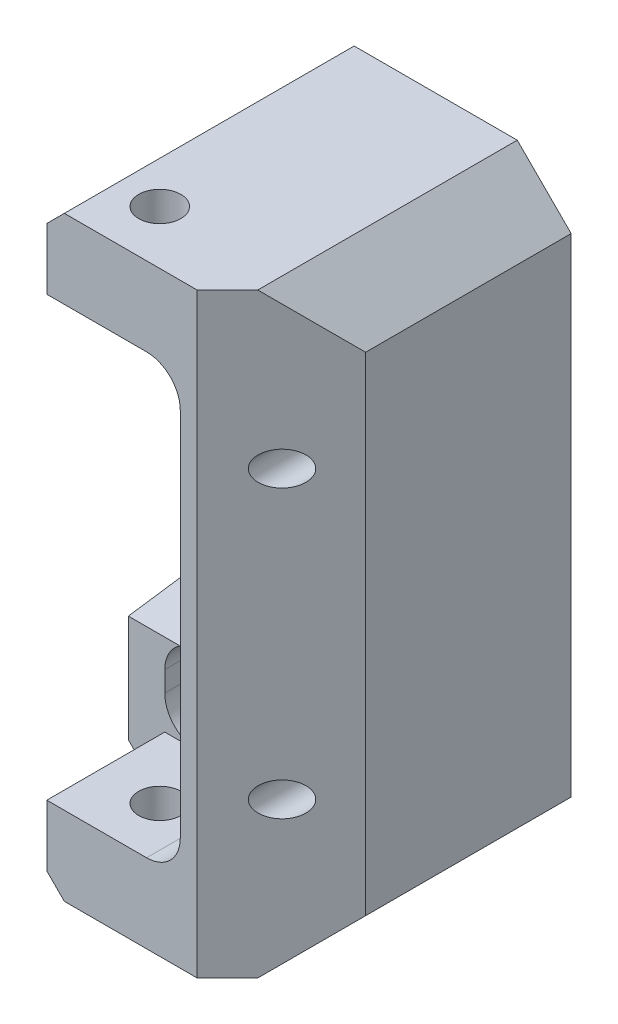
SolidWorks part; units mm, degrees
material "6061-T6 Al"
ref_plane "XY" through (0, 0, 0) normal (0, 0, 1) x (1, 0, 0)
ref_plane "XZ" through (0, 0, 0) normal (0, 1, 0) x (1, 0, 0)
ref_plane "YZ" through (0, 0, 0) normal (1, 0, 0) x (0, 0, -1)
sketch "Sketch1" plane through (0, 0, 0) normal (0, 0, 1) x (1, 0, 0)
  line L0 (-39.9415, 36.195) -> (-51.054, 25.0825)
  line L1 (-51.054, 25.0825) -> (-51.054, 9.4615)
  line L2 (-51.054, 9.4615) -> (-49.53, 7.9375)
  line L3 (-49.53, 7.9375) -> (-34.544, 7.9375)
  line L4 (-34.544, -7.9375) -> (-49.53, -7.9375)
  line L5 (-49.53, -7.9375) -> (-51.054, -9.4615)
  line L6 (-51.054, -9.4615) -> (-51.054, -25.0825)
  line L7 (-51.054, -25.0825) -> (-39.9415, -36.195)
  line L8 (-39.9415, -36.195) -> (-29.0553, -36.195)
  line L9 (-29.0553, -36.195) -> (-26.5414, -34.0179)
  line L10 (-20.2565, -28.575) -> (-4.2023, -28.575)
  line L11 (-4.2023, -28.575) -> (-2.6783, -27.051)
  line L12 (-2.6783, -27.051) -> (-2.6783, -20.7992)
  line L13 (0, -14.1753) -> (0, 14.1753)
  line L14 (-2.6783, 20.7992) -> (-2.6783, 27.051)
  line L15 (-2.6783, 27.051) -> (-4.2023, 28.575)
  line L16 (-4.2023, 28.575) -> (-20.2565, 28.575)
  line L17 (-26.5414, 34.0179) -> (-29.0553, 36.195)
  line L18 (-29.0553, 36.195) -> (-39.9415, 36.195)
  line L19 (-58.9838, 0) -> (23.8466, 0) construction
  arc A0 (-34.544, -7.9375) -> (-34.544, 7.9375) centre (-34.544, 0) ccw
  arc A1 (-20.2565, -28.575) -> (-26.5414, -34.0179) centre (-20.2565, -34.925) ccw
  arc A2 (-26.5414, 34.0179) -> (-20.2565, 28.575) centre (-20.2565, 34.925) ccw
  circle A3 centre (-34.544, 26.035) radius 3.9687
  circle A4 centre (-34.544, -26.035) radius 3.9687
  circle A5 centre (-34.544, -26.035) radius 7.62 construction
  circle A6 centre (-34.544, 26.035) radius 7.62 construction
  ellipse E0 centre (6.8467, -20.7992) end of major axis (6.8061, -30.3273) minor radius 9.525 (0, -14.1753) -> (-2.6783, -20.7992) ccw
  ellipse E1 centre (6.8467, 20.7992) end of major axis (6.8873, 11.2712) minor radius 9.525 (-2.6783, 20.7992) -> (0, 14.1753) ccw
  dimension "D1" = 6.35
  dimension "D2" = 7.9375
  dimension "D21" = 7.9375
  dimension "D22" = 15.24
  dimension "D3" = 51.054
  dimension "D4" = 2.6783
  dimension "D5" = 26.035
  dimension "D6" = 57.15
  dimension "D7" = 45
  dimension "D8" = 1.524
  dimension "D9" = 72.39
  dimension "D10" = 45
  dimension "D11" = 11.1125
  dimension "D12" = 34.544
  dimension "D13" = 45
  dimension "D14" = 1.524
  dimension "D15" = 20.7992
  dimension "D16" = 40.893
  dimension "D17" = 2.1771
  dimension "D18" = 10.8862
  dimension "D19" = 6.8467
  dimension "D20" = 7.7758
sketch "Sketch2" plane through (0, 0, 0) normal (0, 0, 1) x (1, 0, 0)
  circle A0 centre (-34.544, 0) radius 15.875
  dimension "D1" = 31.75
sketch "Sketch3" plane through (0, 0, 0) normal (0, 0, 1) x (1, 0, 0)
  line L0 (-45.6565, 31.5912) -> (-23.4315, 20.4787) construction
  line L1 (-45.6565, 20.4787) -> (-23.4315, 20.4787)
  line L2 (-45.6565, 20.4787) -> (-45.6565, 31.5912)
  line L3 (-45.6565, 31.5912) -> (-23.4315, 31.5912)
  line L4 (-23.4315, 20.4787) -> (-23.4315, 31.5912)
  line L5 (-45.6565, -20.4787) -> (-23.4315, -31.5912) construction
  line L6 (-45.6565, -31.5912) -> (-23.4315, -31.5912)
  line L7 (-45.6565, -31.5912) -> (-45.6565, -20.4787)
  line L8 (-45.6565, -20.4787) -> (-23.4315, -20.4787)
  line L9 (-23.4315, -31.5912) -> (-23.4315, -20.4787)
  dimension "D1" = 11.1125
  dimension "D2" = 22.225
sketch "Sketch5" plane through (0, 0, 0) normal (0, 0, 1) x (1, 0, 0)
  line L0 (0, -56.134) -> (0, 56.134)
  line L1 (-19.05, -34.925) -> (-19.05, 34.925)
  line L2 (-25.4, 41.275) -> (-37.846, 41.275)
  line L3 (-44.196, -34.925) -> (-44.196, -22.606)
  line L4 (-44.196, 34.925) -> (-44.196, 22.606)
  line L5 (-44.196, 22.606) -> (-51.054, 22.606)
  line L6 (-51.054, 25.0825) -> (-51.054, 9.4615) construction
  line L7 (-51.054, 22.606) -> (-51.054, 45.974)
  line L8 (-51.054, 45.974) -> (-40.894, 56.134)
  line L9 (-40.894, 56.134) -> (0, 56.134)
  line L10 (-25.4, -41.275) -> (-37.846, -41.275)
  line L13 (-44.196, -22.606) -> (-51.054, -22.606)
  line L14 (-51.054, -9.4615) -> (-51.054, -25.0825) construction
  line L15 (-51.054, -22.606) -> (-51.054, -45.974)
  line L16 (-51.054, -45.974) -> (-40.894, -56.134)
  line L17 (-40.894, -56.134) -> (0, -56.134)
  line L18 (-58.7902, 0) -> (11.3853, 0) construction
  arc A2 (-19.05, -34.925) -> (-25.4, -41.275) centre (-25.4, -34.925) cw
  arc A3 (-19.05, 34.925) -> (-25.4, 41.275) centre (-25.4, 34.925) ccw
  arc A4 (-37.846, -41.275) -> (-44.196, -34.925) centre (-37.846, -34.925) cw
  arc A5 (-37.846, 41.275) -> (-44.196, 34.925) centre (-37.846, 34.925) ccw
  dimension "D8" = 6.35
  dimension "D6" = 82.55
  dimension "D1" = 19.05
  dimension "D2" = 112.268
  dimension "D3" = 45.212
  dimension "D4" = 45
  dimension "D5" = 6.858
  dimension "D7" = 10.16
extrude "Extrude1" add sketch "Sketch5" along normal blind 54.61
sketch "Sketch6" plane through (0, -56.134, 0) normal (0, -1, 0) x (1, 0, 0)
  line L1 (0, 54.61) -> (0, 0) construction
  line L2 (-40.894, 0) -> (0, 0) construction
  line L4 (-51.054, 54.61) -> (-44.196, 54.61)
  line L5 (-51.054, 54.61) -> (-51.054, 32.385)
  line L6 (-51.054, 32.385) -> (-44.196, 32.385)
  line L7 (-44.196, 54.61) -> (-44.196, 32.385)
  circle A0 centre (-33.02, 44.5008) radius 3.9688
  circle A1 centre (-33.02, 44.5008) radius 10.3187 construction
  dimension "D1" = 7.9375
  dimension "D3" = 20.6375
  dimension "D2" = 44.5008
  dimension "D4" = 22.225
  dimension "D5" = 33.02
  dimension "D6" = 6.858
extrude "Cut-Extrude1" cut sketch "Sketch6" against normal through all
sketch "Sketch8" plane through (0, 0, 32.385) normal (0, 0, 1) x (1, 0, 0)
  line L0 (-37.846, -41.275) -> (-44.196, -41.275)
  line L1 (-44.196, -34.925) -> (-44.196, -22.606) construction
  line L2 (-44.196, -52.832) -> (-44.196, -34.925) construction
  line L3 (-44.196, -41.275) -> (-44.196, -22.606)
  line L4 (-44.196, 34.925) -> (-44.196, 52.832) construction
  line L5 (-44.196, 34.925) -> (-44.196, 41.275)
  line L6 (-37.846, 41.275) -> (-44.196, 41.275)
  line L7 (-44.196, -22.606) -> (-37.846, -22.606)
  line L8 (-37.846, -22.606) -> (-37.846, -41.275)
  line L10 (-51.054, -22.606) -> (-44.196, -22.606) construction
  line L11 (-25.4, -41.275) -> (-37.846, -41.275) construction
  arc A2 (-37.846, 41.275) -> (-44.196, 34.925) centre (-37.846, 34.925) ccw construction
  arc A3 (-37.846, 41.275) -> (-44.196, 34.925) centre (-37.846, 34.925) ccw
extrude "Cut-Extrude2" cut sketch "Sketch8" along normal through all
sketch "Sketch13" plane through (0, 0, 0) normal (0, 0, -1) x (-1, 0, 0)
  line L1 (10.7315, 0) -> (0, 0) construction
  line L2 (0, -56.134) -> (0, 56.134) construction
  circle A0 centre (34.544, 0) radius 23.8125
  dimension "D1" = 47.625
  dimension "D2" = 34.544
extrude "Extrude4" cut sketch "Sketch13" against normal blind 33.02
fillet "Fillet1" radius 6.35 2 edges at (-19.05, -18.0823, 16.51) (-19.05, 18.0823, 16.51)
sketch "pin hole sketch" plane through (0, 0, 0) normal (0, 0, -1) x (-1, 0, 0)
  line L0 (4.2503, 0) -> (33.0535, 0) construction
  line L1 (51.054, 45.974) -> (51.054, 22.606) construction
  circle A0 centre (7.874, 26.9875) radius 3.9688
  circle A1 centre (7.874, -26.9875) radius 3.9688
  dimension "D1" = 7.9375
  dimension "D2" = 53.975
  dimension "D3" = 43.18
sketch "Sketch14" plane through (0, 0, 0) normal (0, 0, -1) x (-1, 0, 0)
  line L0 (44.196, -22.606) -> (51.054, -22.606)
  line L1 (51.054, -22.606) -> (51.054, -24.7675)
  line L2 (44.196, -34.925) -> (44.196, -22.606) construction
  line L3 (44.196, -31.0972) -> (44.196, -22.606)
  line L4 (44.196, -22.606) -> (51.054, -22.606) construction
  arc A0 (44.196, -31.0972) -> (51.054, -24.7675) centre (50.546, -31.0972) cw
  dimension "D1" = 6.35
  dimension "D2" = 6.858
hole_wizard "CBORE for 1/4 Socket Head Cap Screw1" positions "Sketch19" profile "Sketch18" counterbore size "1/4" standard "Ansi Inch"
sketch "Sketch19" plane through (0, 0, 0) normal (0, 0, -1) x (-1, 0, 0)
  line L0 (7.874, 26.9875) -> (7.874, -26.9875) construction
  line L1 (0, 0) -> (7.874, 0) construction
  line L3 (0, -56.134) -> (0, 56.134) construction
  point P0 (7.874, 26.9875)
  point P1 (7.874, -26.9875)
  dimension "D1" = 53.975
  dimension "D2" = 7.874
sketch "Sketch18" plane through (-7.874, 26.9875, 0) normal (1, 0, 0) x (0, 1, 0)
  line L0 (0, 0) -> (0, 21.4347)
  line L1 (0, 21.4347) -> (3.9687, 19.05)
  line L2 (3.9687, 19.05) -> (3.9687, 2.8448)
  line L3 (3.9687, 2.8448) -> (3.9878, 2.8448)
  line L5 (3.9878, 2.8448) -> (3.9878, 0.3683)
  line L6 (3.9878, 0.3683) -> (4.3561, 0)
  line L7 (4.3561, 0) -> (0, 0)
  line L8 (-3.9878, 0.3683) -> (-4.3561, 0) construction
  line L10 (0, 21.4347) -> (-3.9688, 19.05) construction
  line L11 (0, -6.35) -> (0, 107.95) construction
  dimension "Hole Dia." = 7.9375
  dimension "Hole Depth" = 19.05
  dimension "C'Bore Dia." = 7.9756
  dimension "C'Bore Depth" = 2.8448
  dimension "Near C'Sink Dia." = 8.7122
  dimension "Near C'Sink Angle" = 90
  dimension "Drill Angle" = 118
chamfer "Chamfer4" distance 10.16 2 edges at (0, -56.134, 27.305) (0, 56.134, 27.305)
chamfer "Chamfer7" distance 15.875 angle 45 1 edges at (0, 0, 54.61)
sketch "Sketch22" plane through (0, 0, 0) normal (0, 0, -1) x (-1, 0, 0)
  line L0 (38.354, -24.765) -> (38.354, -22.606)
  line L1 (38.354, -22.606) -> (44.196, -22.606)
  line L2 (44.196, -22.606) -> (44.196, -31.0946)
  line L4 (44.196, -34.925) -> (44.196, -22.606) construction
  line L6 (44.196, -22.606) -> (51.054, -22.606) construction
  arc A0 (44.196, -31.0946) -> (38.354, -24.765) centre (37.846, -31.0946) ccw
  dimension "D1" = 6.35
  dimension "D2" = 5.842
  dimension "D3" = 2.159
  dimension "D4" = 8.4886
hole_wizard "1/4 (0.25) Diameter Hole1" positions "Sketch21" profile "Sketch20" hole size "1/4" standard "Ansi Inch" end condition through all
sketch "Sketch21" plane through (0, 0, 0) normal (0, 0, -1) x (-1, 0, 0)
  point P0 (7.874, 26.9875)
  point P1 (7.874, -26.9875)
sketch "Sketch20" plane through (-7.874, 26.9875, 0) normal (1, 0, 0) x (0, 1, 0)
  line L0 (0, 0) -> (0, 54.61)
  line L1 (0, 54.61) -> (3.175, 54.61)
  line L2 (3.175, 54.61) -> (3.175, 0)
  line L5 (3.175, 0) -> (0, 0)
  line L11 (0, -6.35) -> (0, 107.95) construction
  dimension "Thru Hole Dia." = 6.35
  dimension "Thru Hole Depth" = 54.61
extrude "Extrude9" add sketch "Sketch22" against normal up to surface (32.385 mm away) up to face at (-45.4362, -37.544, 32.385)
mirror "Mirror3" about plane through (0, 0, 0) normal (0, 1, 0) of "Extrude9"
sketch "Sketch17" plane through (-51.054, 0, 0) normal (-1, 0, 0) x (0, 0, 1)
  line L0 (32.385, -25.781) -> (32.385, -22.606)
  line L1 (32.385, -22.606) -> (32.385, -45.974) construction
  line L2 (32.385, -22.606) -> (10.16, -22.606)
  line L3 (32.385, -22.606) -> (0, -22.606) construction
  line L4 (10.16, -22.606) -> (32.385, -25.781)
  line L5 (0, 0) -> (79.2407, 0) construction
  line L6 (32.385, 25.781) -> (32.385, 22.606)
  line L7 (32.385, 22.606) -> (10.16, 22.606)
  line L8 (10.16, 22.606) -> (32.385, 25.781)
  dimension "D1" = 22.225
  dimension "D2" = 3.175
extrude "Extrude8" cut sketch "Sketch17" against normal blind 17.62
ref_point "Point1"
ref_plane "CENTER AXIS PLANE" through (-33.02, 0, 0) normal (1, 0, 0) x (0, 0, -1)
